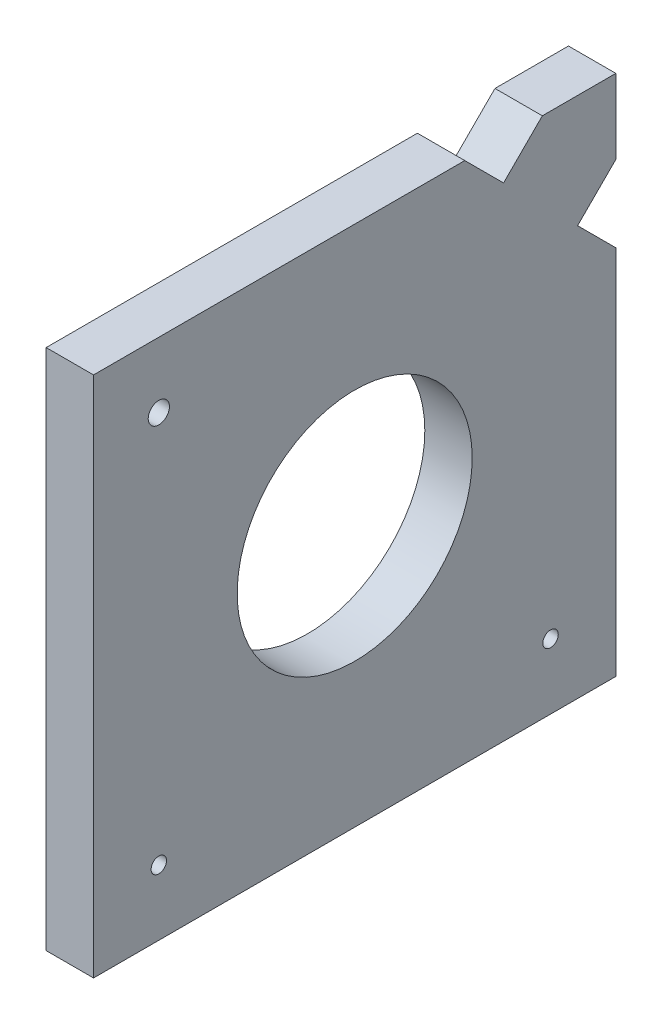
SolidWorks part; units mm, degrees
ref_plane "Front Plane" through (0, 0, 0) normal (0, 0, 1) x (1, 0, 0)
ref_plane "Top Plane" through (0, 0, 0) normal (0, 1, 0) x (1, 0, 0)
ref_plane "Right Plane" through (0, 0, 0) normal (1, 0, 0) x (0, 0, -1)
sketch "Sketch1" plane through (0, 0, 0) normal (1, 0, 0) x (0, 0, -1)
  line L0 (35, 70) -> (35, 0) construction
  line L1 (0, 0) -> (70, 0)
  line L2 (0, 0) -> (0, 70)
  line L3 (0, 70) -> (49.7566, 70)
  line L4 (70, 70) -> (70, 60.0116)
  line L5 (0, 35) -> (70, 35) construction
  line L6 (64.8725, 54.8841) -> (70, 49.7566)
  line L7 (54.9526, 64.804) -> (60.1486, 70)
  line L8 (70, 60.0116) -> (64.8725, 54.8841)
  line L10 (60.1486, 70) -> (70, 70)
  line L11 (70, 49.7566) -> (70, 0)
  line L12 (54.9526, 64.804) -> (49.7566, 70)
  circle A0 centre (35, 35) radius 15.748
extrude "Boss-Extrude1" add sketch "Sketch1" along normal blind 6.35
sketch "Sketch2" plane through (6.35, 0, 0) normal (1, 0, 0) x (0, 0, -1)
  circle A0 centre (8.75, 61.25) radius 1.4224
  circle A1 centre (8.75, 8.75) radius 1.0325
  circle A2 centre (61.25, 8.75) radius 1.0325
extrude "Cut-Extrude1" cut sketch "Sketch2" against normal blind 6.35
sketch "Sketch3" plane through (6.35, 0, 0) normal (1, 0, 0) x (0, 0, -1)
  line L0 (70, 70) -> (46.1355, 46.1355)
  circle A0 centre (35, 35) radius 15.748 construction
